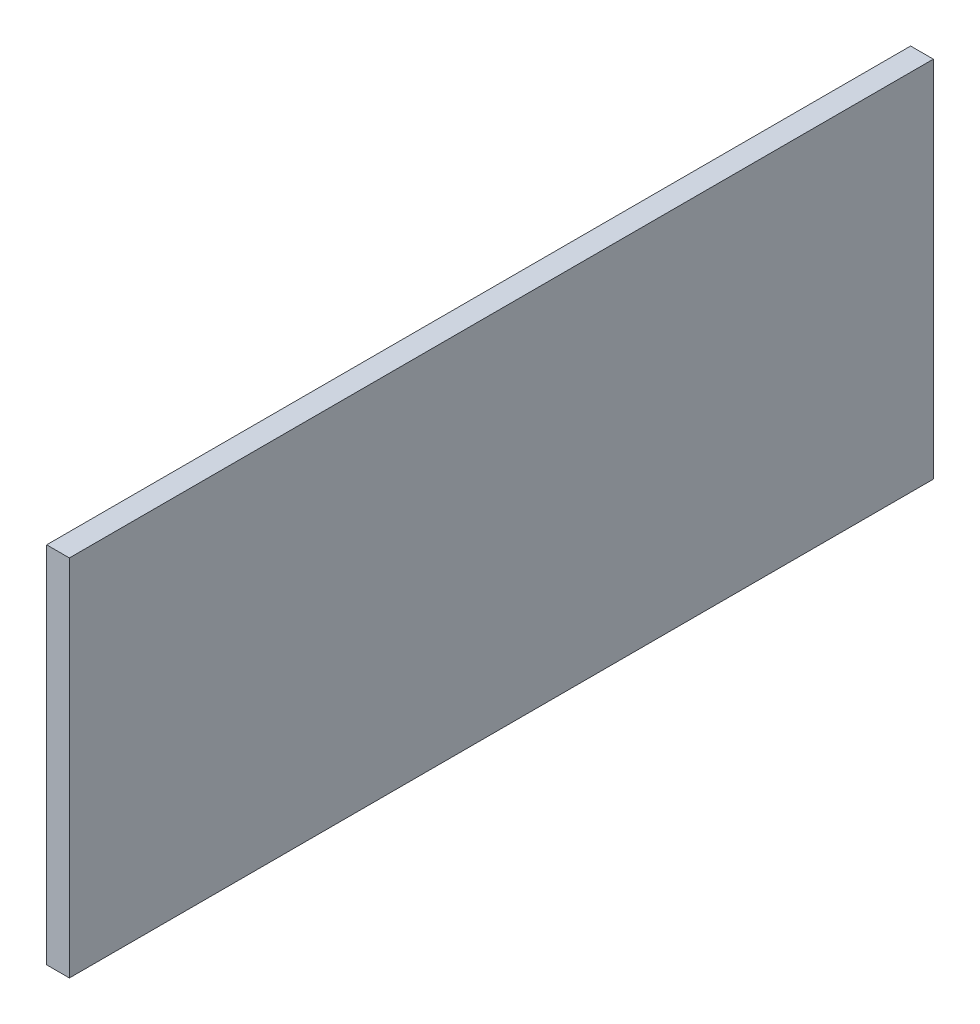
SolidWorks part; units mm, degrees
material "1060 Alloy"
ref_plane "Front Plane" through (0, 0, 0) normal (0, 0, 1) x (1, 0, 0)
ref_plane "Top Plane" through (0, 0, 0) normal (0, 1, 0) x (1, 0, 0)
ref_plane "Right Plane" through (0, 0, 0) normal (1, 0, 0) x (0, 0, -1)
sketch "Sketch1" plane through (0, 0, 0) normal (0, 1, 0) x (1, 0, 0)
  line L1 (101.6, -60.325) -> (-101.6, -60.325)
  line L2 (101.6, -60.325) -> (101.6, 60.325)
  line L3 (101.6, 60.325) -> (-101.6, 60.325)
  line L4 (-101.6, -60.325) -> (-101.6, 60.325)
  line L5 (101.6, -60.325) -> (-101.6, 60.325) construction
  line L6 (101.6, 60.325) -> (-101.6, -60.325) construction
  point P0 (0, 0)
  dimension "D1" = 120.65
  dimension "D2" = 203.2
extrude "Boss-Extrude1" add sketch "Sketch1" along normal blind 50.8
sketch "Sketch2" plane through (0, 50.8, 0) normal (0, 1, 0) x (1, 0, 0)
  line L8 (-98.425, 57.15) -> (-98.425, -57.15)
  line L9 (98.425, 57.15) -> (-98.425, 57.15)
  line L10 (98.425, -57.15) -> (98.425, 57.15)
  line L11 (-98.425, -57.15) -> (98.425, -57.15)
  line L12 (-98.425, 57.15) -> (-98.425, -57.15)
  line L13 (98.425, 57.15) -> (-98.425, 57.15)
  line L14 (98.425, -57.15) -> (98.425, 57.15)
  line L15 (-98.425, -57.15) -> (98.425, -57.15)
  dimension "D1" = 3.175
extrude "Cut-Extrude1" cut sketch "Sketch2" against normal through all
sketch "Sketch4" plane through (0, 50.8, 0) normal (0, 1, 0) x (1, 0, 0)
  line L4 (101.6, 60.325) -> (-101.6, 60.325)
  line L5 (-101.6, 60.325) -> (-101.6, -60.325)
  line L6 (-101.6, -60.325) -> (101.6, -60.325)
  line L7 (101.6, -60.325) -> (101.6, 60.325)
  line L9 (-98.425, -57.15) -> (98.425, -57.15)
  line L10 (-98.425, -57.15) -> (-98.425, 57.15)
  line L11 (-98.425, 57.15) -> (98.425, 57.15)
  line L12 (98.425, -57.15) -> (98.425, 57.15)
  line L13 (-98.425, -57.15) -> (98.425, 57.15) construction
  line L14 (-98.425, 57.15) -> (98.425, -57.15) construction
  point P12 (0, 0)
  dimension "D1" = 3.175
  dimension "D2" = 3.175
  dimension "D3" = 3.175
  dimension "D4" = 3.175
extrude "Boss-Extrude2" add sketch "Sketch4" against normal blind 6.35
sketch "Sketch10" plane through (0, 0, 60.325) normal (0, 0, 1) x (1, 0, 0)
  line L0 (0, 22.225) -> (50.8, 22.225) construction
  line L1 (-101.6, 0) -> (101.6, 0) construction
  line L3 (-104.775, 13.4874) -> (104.775, 13.4874)
  line L6 (50.8, 22.225) -> (101.6, 22.225) construction
  line L7 (101.6, 50.8) -> (101.6, 0) construction
  line L8 (0, 22.225) -> (-50.8, 22.225) construction
  line L9 (-50.8, 22.225) -> (-101.6, 22.225) construction
  line L10 (-101.6, 50.8) -> (-101.6, 0) construction
  circle A0 centre (-76.2, 22.225) radius 10.2489
  circle A1 centre (-25.4, 22.225) radius 10.2489
  circle A2 centre (25.4, 22.225) radius 10.2489
  circle A3 centre (76.2, 22.225) radius 10.2489
  point P5 (-76.2, 22.225)
  point P9 (-25.4, 22.225)
  point P12 (25.4, 22.225)
  point P13 (76.2, 22.225)
  dimension "D2" = 22.225
  dimension "D1" = 20.4978
  dimension "D3" = 8.7376
extrude "Cut-Extrude5" cut sketch "Sketch10" against normal through all
sketch "Sketch12" plane through (101.6, 0, 0) normal (1, 0, 0) x (0, 0, -1)
  line L0 (60.325, 28.575) -> (-60.325, 28.575) construction
  line L1 (60.325, 50.8) -> (60.325, 0) construction
  line L2 (-60.325, 50.8) -> (-60.325, 0) construction
  line L3 (-60.325, 0) -> (60.325, 0) construction
  line L4 (-60.325, 19.8374) -> (60.325, 19.8374)
  circle A0 centre (-25.4, 28.575) radius 10.2489
  circle A1 centre (25.4, 28.575) radius 10.2489
  point P6 (60.325, 28.575)
  point P7 (-25.4, 28.575)
  point P10 (25.4, 28.575)
  dimension "D2" = 8.7376
  dimension "D3" = 20.4978
  dimension "D5" = 28.575
  dimension "D1" = 34.925
  dimension "D4" = 34.925
extrude "Cut-Extrude6" cut sketch "Sketch12" against normal up to next
sketch "Sketch13" plane through (-101.6, 0, 0) normal (-1, 0, 0) x (0, 0, 1)
  line L0 (60.325, 25.4) -> (-60.325, 25.4) construction
  line L1 (60.325, 50.8) -> (60.325, 0) construction
  line L2 (-60.325, 50.8) -> (-60.325, 0) construction
  line L4 (-60.325, 50.8) -> (60.325, 50.8) construction
  circle A0 centre (15.875, 28.575) radius 12.554
  point P6 (22.225, 25.4)
  point P7 (15.875, 28.575)
  dimension "D3" = 25.1079
  dimension "D4" = 22.225
  dimension "D1" = 38.1
  dimension "D2" = 76.2
extrude "Cut-Extrude7" cut sketch "Sketch13" against normal up to next
sketch "Sketch14" plane through (0, 50.8, 0) normal (0, 1, 0) x (1, 0, 0)
  line L0 (101.6, 60.325) -> (-101.6, 60.325) construction
  line L2 (98.425, 60.325) -> (-101.6, 60.325)
  line L3 (98.425, 60.325) -> (98.425, -60.325)
  line L4 (98.425, -60.325) -> (-101.6, -60.325)
  line L6 (-101.6, 60.325) -> (-101.6, -60.325)
  line L7 (101.6, -60.325) -> (101.6, 60.325) construction
  dimension "D1" = 3.175
extrude "Cut-Extrude8" cut sketch "Sketch14" against normal through all
sketch "Sketch15" plane through (101.6, 0, 0) normal (1, 0, 0) x (0, 0, -1)
  line L0 (20.0433, 19.8374) -> (30.7567, 19.8374) construction
  line L1 (-30.7567, 19.8374) -> (-20.0433, 19.8374) construction
  line L2 (20.0433, 19.8374) -> (30.7567, 19.8374)
  line L3 (-30.7567, 19.8374) -> (-20.0433, 19.8374)
  arc A0 (-20.0433, 19.8374) -> (-30.7567, 19.8374) centre (-25.4, 28.575) ccw construction
  arc A1 (30.7567, 19.8374) -> (20.0433, 19.8374) centre (25.4, 28.575) ccw construction
  arc A2 (-20.0433, 19.8374) -> (-30.7567, 19.8374) centre (-25.4, 28.575) ccw
  arc A3 (30.7567, 19.8374) -> (20.0433, 19.8374) centre (25.4, 28.575) ccw
extrude "Boss-Extrude3" add sketch "Sketch15" against normal up to surface (3.175 mm away) up to face at (98.425, 29.3306, -25.4)
